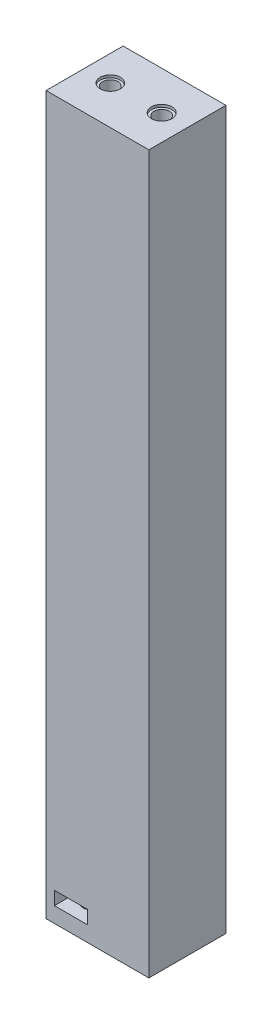
SolidWorks part; units mm, degrees
ref_plane "Front Plane" through (0, 0, 0) normal (0, 0, 1) x (1, 0, 0)
ref_plane "Top Plane" through (0, 0, 0) normal (0, 1, 0) x (1, 0, 0)
ref_plane "Right Plane" through (0, 0, 0) normal (1, 0, 0) x (0, 0, -1)
sketch "Sketch1" plane through (0, 0, 0) normal (0, 1, 0) x (1, 0, 0)
  line L3 (-8.2, -3.5) -> (-8.2, -7.4071)
  line L5 (-1.8, -3.5) -> (-1.8, -7.4071)
  line L7 (-5, 0.15) -> (-8.2, 0.15)
  line L8 (-8.2, 0.15) -> (-8.2, -3.5)
  line L9 (-5, 0.15) -> (-1.8, 0.15)
  line L10 (-1.8, 0.15) -> (-1.8, -3.5)
  line L11 (10.1859, 3.5) -> (10.1859, -11.2951)
  line L12 (5.1859, 7.5929) -> (-9.8141, 7.5929)
  line L13 (-9.8141, 7.5929) -> (-9.8141, -7.4071)
  line L14 (-9.8141, -7.4071) -> (10.1859, -7.4071)
  line L15 (10.1859, -7.4071) -> (10.1859, 7.5929)
  line L16 (10.1859, 7.5929) -> (5.1859, 7.5929)
  line L27 (8.2, 3.5) -> (8.2, 7.5929)
  line L28 (1.8, 3.5) -> (1.8, 7.5929)
  line L30 (5, -0.15) -> (8.2, -0.15)
  line L31 (8.2, -0.15) -> (8.2, 3.5)
  line L32 (5, -0.15) -> (1.8, -0.15)
  line L33 (1.8, -0.15) -> (1.8, 3.5)
  circle A0 centre (5, 3.5) radius 1.5
  circle A1 centre (-5, -3.5) radius 1.5
extrude "Boss-Extrude1" add sketch "Sketch1" along normal blind 2.6 contours L32 L33 L28 L12 L13 L14 L3 L8 L7 L9 L10 L5 L11 L15 L16 L27 L31 L30
sketch "Sketch2" plane through (0, 0, 0) normal (0, -1, 0) x (1, 0, 0)
  line L0 (8.2, -3.5) -> (8.2, -7.5929) construction
  line L1 (8.2, 0.15) -> (8.2, -3.5) construction
  line L2 (5, 0.15) -> (8.2, 0.15) construction
  line L3 (5, 0.15) -> (1.8, 0.15) construction
  line L4 (1.8, 0.15) -> (1.8, -3.5) construction
  line L5 (-9.8141, 7.4071) -> (-9.8141, -7.5929)
  line L6 (10.1859, 7.4071) -> (-9.8141, 7.4071)
  line L7 (10.1859, -7.5929) -> (10.1859, 7.4071)
  line L8 (5.1859, -7.5929) -> (10.1859, -7.5929)
  line L9 (-9.8141, -7.5929) -> (5.1859, -7.5929)
  line L10 (-9.8141, 7.4071) -> (-9.8141, -7.5929)
  line L11 (10.1859, 7.4071) -> (-9.8141, 7.4071)
  line L12 (10.1859, -7.5929) -> (10.1859, 7.4071)
  line L13 (5.1859, -7.5929) -> (10.1859, -7.5929)
  line L14 (-9.8141, -7.5929) -> (5.1859, -7.5929)
  line L15 (1.8, -3.5) -> (1.8, -7.5929) construction
  line L16 (10.1859, -3.5) -> (10.1859, 11.2951) construction
  line L17 (-1.8, 3.5) -> (-1.8, 7.4071) construction
  line L18 (-1.8, -0.15) -> (-1.8, 3.5) construction
  line L19 (-5, -0.15) -> (-1.8, -0.15) construction
  line L20 (-5, -0.15) -> (-8.2, -0.15) construction
  line L21 (-8.2, -0.15) -> (-8.2, 3.5) construction
  line L22 (-8.2, 3.5) -> (-8.2, 7.4071) construction
  line L23 (8.2, -3.5) -> (8.2, -7.5929)
  line L24 (8.2, 0.15) -> (8.2, -3.5)
  line L25 (5, 0.15) -> (8.2, 0.15)
  line L26 (5, 0.15) -> (1.8, 0.15)
  line L27 (1.8, 0.15) -> (1.8, -3.5)
  line L28 (1.8, -3.5) -> (1.8, -7.5929)
  line L29 (10.1859, -3.5) -> (10.1859, 11.2951)
  line L30 (-1.8, 3.5) -> (-1.8, 7.4071)
  line L31 (-1.8, -0.15) -> (-1.8, 3.5)
  line L32 (-5, -0.15) -> (-1.8, -0.15)
  line L33 (-5, -0.15) -> (-8.2, -0.15)
  line L34 (-8.2, -0.15) -> (-8.2, 3.5)
  line L35 (-8.2, 3.5) -> (-8.2, 7.4071)
  circle A1 centre (-5, 3.5) radius 1.5
  circle A2 centre (-5, 3.5) radius 1.5
  circle A3 centre (5, -3.5) radius 1.5
  circle A4 centre (5, -3.5) radius 1.5
  line M8 (1.8, 0.15) -> (8.2, 0.15)
  line M9 (8.2, 0.15) -> (8.2, -7.5929)
  line M10 (8.2, -7.5929) -> (10.1859, -7.5929)
  line M11 (10.1859, -7.5929) -> (10.1859, 7.4071)
  line M12 (10.1859, 7.4071) -> (-1.8, 7.4071)
  line M13 (-1.8, 7.4071) -> (-1.8, -0.15)
  line M14 (-1.8, -0.15) -> (-8.2, -0.15)
  line M15 (-8.2, -0.15) -> (-8.2, 7.4071)
  line M16 (-8.2, 7.4071) -> (-9.8141, 7.4071)
  line M17 (-9.8141, 7.4071) -> (-9.8141, -7.5929)
  line M18 (-9.8141, -7.5929) -> (1.8, -7.5929)
  line M19 (1.8, -7.5929) -> (1.8, 0.15)
  dimension "D1" = 0
  dimension "D2" = 0
  dimension "D3" = 0
extrude "Boss-Extrude2" add sketch "Sketch2" along normal blind 3 contours L12 M19 M8 M9 M10 M11 M12 M13 M14 M15 M16 M17 M18 | L14 L13 A4 M19 M9 M8 | L11 A2 M13 M15 M14
sketch "Sketch3" plane through (0, 2.6, 0) normal (0, 1, 0) x (1, 0, 0)
  line L0 (8.2, 3.5) -> (8.2, 7.5929) construction
  line L1 (8.2, -0.15) -> (8.2, 3.5) construction
  line L2 (5, -0.15) -> (8.2, -0.15) construction
  line L3 (5, -0.15) -> (1.8, -0.15) construction
  line L4 (1.8, -0.15) -> (1.8, 3.5) construction
  line L5 (-9.8141, 7.5929) -> (-9.8141, -7.4071)
  line L6 (-9.8141, -7.4071) -> (10.1859, -7.4071)
  line L7 (10.1859, -7.4071) -> (10.1859, 7.5929)
  line L8 (10.1859, 7.5929) -> (5.1859, 7.5929)
  line L9 (5.1859, 7.5929) -> (-9.8141, 7.5929)
  line L10 (-9.8141, 7.5929) -> (-9.8141, -7.4071)
  line L11 (-9.8141, -7.4071) -> (10.1859, -7.4071)
  line L12 (10.1859, -7.4071) -> (10.1859, 7.5929)
  line L13 (10.1859, 7.5929) -> (5.1859, 7.5929)
  line L14 (5.1859, 7.5929) -> (-9.8141, 7.5929)
  line L15 (1.8, 3.5) -> (1.8, 7.5929) construction
  line L16 (10.1859, 3.5) -> (10.1859, -11.2951) construction
  line L17 (-1.8, -3.5) -> (-1.8, -7.4071) construction
  line L18 (-1.8, 0.15) -> (-1.8, -3.5) construction
  line L19 (-5, 0.15) -> (-1.8, 0.15) construction
  line L20 (-5, 0.15) -> (-8.2, 0.15) construction
  line L21 (-8.2, 0.15) -> (-8.2, -3.5) construction
  line L22 (-8.2, -3.5) -> (-8.2, -7.4071) construction
  line L23 (8.2, 3.5) -> (8.2, 7.5929)
  line L24 (8.2, -0.15) -> (8.2, 3.5)
  line L25 (5, -0.15) -> (8.2, -0.15)
  line L26 (5, -0.15) -> (1.8, -0.15)
  line L27 (1.8, -0.15) -> (1.8, 3.5)
  line L28 (1.8, 3.5) -> (1.8, 7.5929)
  line L29 (10.1859, 3.5) -> (10.1859, -11.2951)
  line L30 (-1.8, -3.5) -> (-1.8, -7.4071)
  line L31 (-1.8, 0.15) -> (-1.8, -3.5)
  line L32 (-5, 0.15) -> (-1.8, 0.15)
  line L33 (-5, 0.15) -> (-8.2, 0.15)
  line L34 (-8.2, 0.15) -> (-8.2, -3.5)
  line L35 (-8.2, -3.5) -> (-8.2, -7.4071)
  circle A1 centre (-5, -3.5) radius 1.5
  circle A2 centre (-5, -3.5) radius 1.5
  circle A3 centre (5, 3.5) radius 1.5
  circle A4 centre (5, 3.5) radius 1.5
  dimension "D1" = 0
  dimension "D2" = 0
  dimension "D3" = 0
sketch "Sketch6" plane through (0, 2.6, 0) normal (0, 1, 0) x (1, 0, 0)
  line L0 (8.2, 3.5) -> (8.2, 7.5929) construction
  line L1 (8.2, -0.15) -> (8.2, 3.5) construction
  line L2 (5, -0.15) -> (8.2, -0.15) construction
  line L3 (5, -0.15) -> (1.8, -0.15) construction
  line L4 (1.8, -0.15) -> (1.8, 3.5) construction
  line L5 (-9.8141, 7.5929) -> (-9.8141, -7.4071)
  line L6 (-9.8141, -7.4071) -> (10.1859, -7.4071)
  line L7 (10.1859, -7.4071) -> (10.1859, 7.5929)
  line L8 (10.1859, 7.5929) -> (5.1859, 7.5929)
  line L9 (5.1859, 7.5929) -> (-9.8141, 7.5929)
  line L10 (-9.8141, 7.5929) -> (-9.8141, -7.4071)
  line L11 (-9.8141, -7.4071) -> (10.1859, -7.4071)
  line L12 (10.1859, -7.4071) -> (10.1859, 7.5929)
  line L13 (10.1859, 7.5929) -> (5.1859, 7.5929)
  line L14 (5.1859, 7.5929) -> (-9.8141, 7.5929)
  line L15 (1.8, 3.5) -> (1.8, 7.5929) construction
  line L16 (-1.8, -3.5) -> (-1.8, -7.4071) construction
  line L17 (-1.8, 0.15) -> (-1.8, -3.5) construction
  line L18 (-5, 0.15) -> (-1.8, 0.15) construction
  line L19 (-5, 0.15) -> (-8.2, 0.15) construction
  line L20 (-8.2, 0.15) -> (-8.2, -3.5) construction
  line L21 (-8.2, -3.5) -> (-8.2, -7.4071) construction
  line L22 (10.1859, 3.5) -> (10.1859, -11.2951) construction
  line L23 (8.2, 3.5) -> (8.2, 7.5929)
  line L24 (8.2, -0.15) -> (8.2, 3.5)
  line L25 (5, -0.15) -> (8.2, -0.15)
  line L26 (5, -0.15) -> (1.8, -0.15)
  line L27 (1.8, -0.15) -> (1.8, 3.5)
  line L28 (1.8, 3.5) -> (1.8, 7.5929)
  line L29 (-1.8, -3.5) -> (-1.8, -7.4071)
  line L30 (-1.8, 0.15) -> (-1.8, -3.5)
  line L31 (-5, 0.15) -> (-1.8, 0.15)
  line L32 (-5, 0.15) -> (-8.2, 0.15)
  line L33 (-8.2, 0.15) -> (-8.2, -3.5)
  line L34 (-8.2, -3.5) -> (-8.2, -7.4071)
  line L35 (10.1859, 3.5) -> (10.1859, -11.2951)
  circle A1 centre (5, 3.5) radius 1.5
  circle A2 centre (5, 3.5) radius 1.5
  circle A3 centre (-5, -3.5) radius 1.5
  circle A4 centre (-5, -3.5) radius 1.5
  line M8 (8.2, -0.15) -> (1.8, -0.15)
  line M9 (1.8, -0.15) -> (1.8, 7.5929)
  line M10 (1.8, 7.5929) -> (-9.8141, 7.5929)
  line M11 (-9.8141, 7.5929) -> (-9.8141, -7.4071)
  line M12 (-9.8141, -7.4071) -> (-8.2, -7.4071)
  line M13 (-8.2, -7.4071) -> (-8.2, 0.15)
  line M14 (-8.2, 0.15) -> (-1.8, 0.15)
  line M15 (-1.8, 0.15) -> (-1.8, -7.4071)
  line M16 (-1.8, -7.4071) -> (10.1859, -7.4071)
  line M17 (10.1859, -7.4071) -> (10.1859, 7.5929)
  line M18 (10.1859, 7.5929) -> (8.2, 7.5929)
  line M19 (8.2, 7.5929) -> (8.2, -0.15)
  dimension "D1" = 0
  dimension "D2" = 0
  dimension "D3" = 0
extrude "Boss-Extrude3" add sketch "Sketch6" along normal blind 134 contours L11 A4 M13 M15 M14 | L13 L14 A2 M9 M8 M19 | L12 M19 M8 M9 M10 M11 M12 M13 M14 M15 M16 M17 M18 | A4 | A2
sketch "Sketch8" plane through (0, -3, 0) normal (0, -1, 0) x (1, 0, 0)
  circle A0 centre (-5, 3.5) radius 1.5
  circle A1 centre (5, -3.5) radius 1.5
extrude "Cut-Extrude1" cut sketch "Sketch8" against normal blind 19.5
sketch "Sketch9" plane through (0, 136.6, 0) normal (0, 1, 0) x (1, 0, 0)
  line L0 (10.1859, 7.5929) -> (10.1859, 0.0929)
  line L1 (10.1859, 0.0929) -> (0.1859, 0.0929)
  line L2 (10.1859, -7.4071) -> (10.1859, 7.5929) construction
  line L3 (0.1859, 0.0929) -> (-4.8141, 0.0929)
  line L4 (0.1859, 0.0929) -> (5.1859, 0.0929)
  circle A0 centre (-4.8141, 0.0929) radius 1.5
  circle A1 centre (5.1859, 0.0929) radius 1.5
extrude "Cut-Extrude2" cut sketch "Sketch9" against normal blind 7
sketch "Sketch10" plane through (0, 136.6, 0) normal (0, 1, 0) x (1, 0, 0)
  circle A0 centre (-4.8141, 0.0929) radius 1.965
  circle A1 centre (5.1859, 0.0929) radius 2
extrude "Cut-Extrude4" cut sketch "Sketch10" against normal blind 0.5
